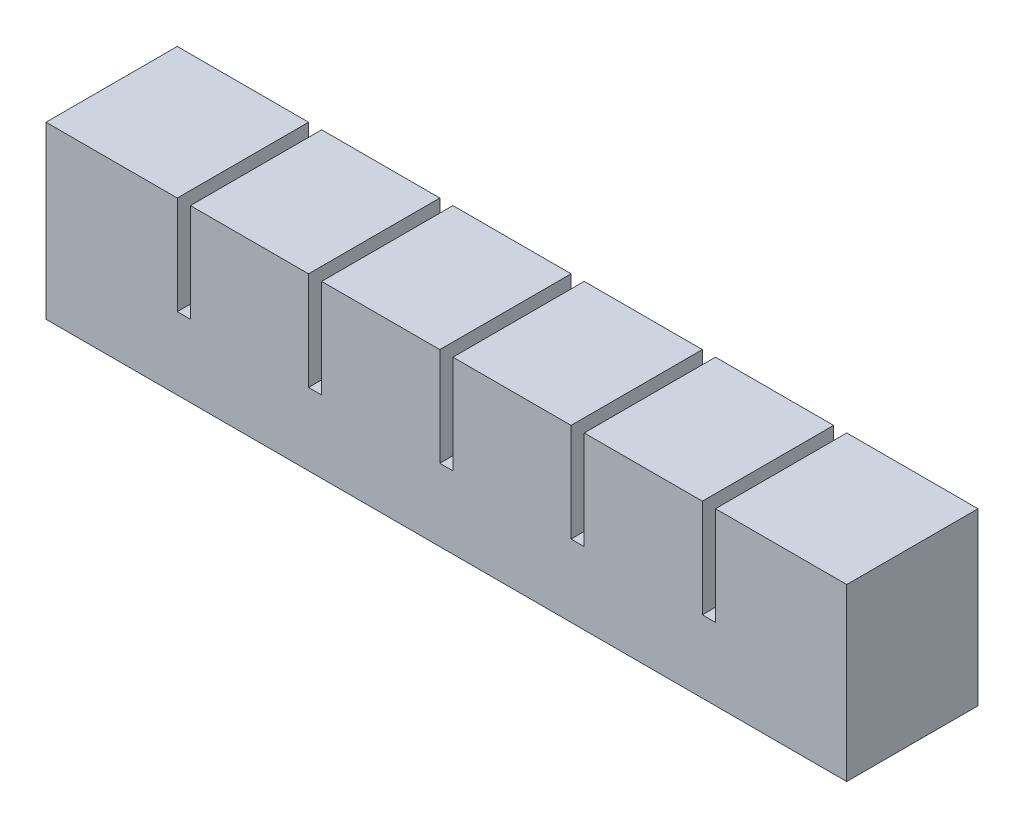
SolidWorks part; units mm, degrees
ref_plane "Front Plane" through (0, 0, 0) normal (0, 0, 1) x (1, 0, 0)
ref_plane "Top Plane" through (0, 0, 0) normal (0, 1, 0) x (1, 0, 0)
ref_plane "Right Plane" through (0, 0, 0) normal (1, 0, 0) x (0, 0, -1)
sketch "Sketch1" plane through (0, 0, 0) normal (0, 0, 1) x (1, 0, 0)
  line L1 (0, 0) -> (18, 0)
  line L2 (0, 0) -> (0, 20)
  line L3 (0, 20) -> (18, 20)
  line L4 (18, 0) -> (18, 20)
  dimension "D1" = 18
  dimension "D2" = 20
extrude "Boss-Extrude1" add sketch "Sketch1" along normal blind 20
sketch "Sketch2" plane through (0, 0, 0) normal (0, -1, 0) x (1, 0, 0)
  line L0 (18, 20) -> (18, 0) construction
  line L1 (6, 14) -> (12, 14)
  line L2 (6, 14) -> (6, 6)
  line L3 (6, 6) -> (12, 6)
  line L4 (12, 14) -> (12, 6)
  line L5 (0, 20) -> (18, 20) construction
  line L6 (0, 20) -> (0, 0) construction
  line L7 (0, 0) -> (18, 0) construction
  dimension "D1" = 6
  dimension "D2" = 6
  dimension "D3" = 6
  dimension "D4" = 6
extrude "Cut-Extrude1" cut sketch "Sketch2" against normal blind 14
sketch "Sketch3" plane through (18, 0, 0) normal (1, 0, 0) x (0, 0, -1)
  line L0 (0, 0) -> (0, 20) construction
  line L1 (-20, 0) -> (0, 0)
  line L2 (-20, 0) -> (-20, 5)
  line L3 (-20, 5) -> (0, 5)
  line L4 (0, 0) -> (0, 5)
  dimension "D1" = 5
extrude "Boss-Extrude2" add sketch "Sketch3" along normal blind 2
pattern_linear "LPattern1" count 6 spacing 20 along (1, 0, 0) of bodies 103
sketch "Sketch4" plane through (118, 0, 0) normal (1, 0, 0) x (0, 0, -1)
  line L1 (-20, 5) -> (0, 5)
  line L2 (-20, 5) -> (-20, 20)
  line L3 (-20, 20) -> (0, 20)
  line L4 (0, 5) -> (0, 20)
extrude "Boss-Extrude3" add sketch "Sketch4" along normal up to surface (2 mm away) up to face at (120, 2.5, 10)
sketch "Sketch5" plane through (0, 0, 0) normal (-1, 0, 0) x (0, 0, 1)
  line L1 (0, 0) -> (20, 0)
  line L2 (0, 0) -> (0, 20)
  line L3 (0, 20) -> (20, 20)
  line L4 (20, 0) -> (20, 20)
extrude "Boss-Extrude4" add sketch "Sketch5" along normal blind 2
combine bodies "Combine1" operation type add bodies to combine 104 105 106 107 109 110
ref_point "Point1"
sketch "Sketch7" plane through (0, 0, 0) normal (0, -1, 0) x (-1, 0, 0)
  line L0 (-112, -6) -> (-112, -14) construction
  line L1 (-6, -9) -> (-112, -9)
  line L2 (-6, -9) -> (-6, -11)
  line L3 (-6, -11) -> (-112, -11)
  line L4 (-112, -9) -> (-112, -11)
  line L5 (-6, -9) -> (-112, -11) construction
  line L6 (-6, -11) -> (-112, -9) construction
  point P0 (-59, -10)
  dimension "D1" = 2
extrude "Cut-Extrude2" cut sketch "Sketch7" against normal blind 2
sketch "Sketch8" plane through (0, 0, 0) normal (0, -1, 0) x (-1, 0, 0)
  line L1 (2, -20) -> (-120, -20)
  line L2 (2, -20) -> (2, 0)
  line L3 (2, 0) -> (-120, 0)
  line L4 (-120, -20) -> (-120, 0)
extrude "Boss-Extrude5" add sketch "Sketch8" along normal blind 6
